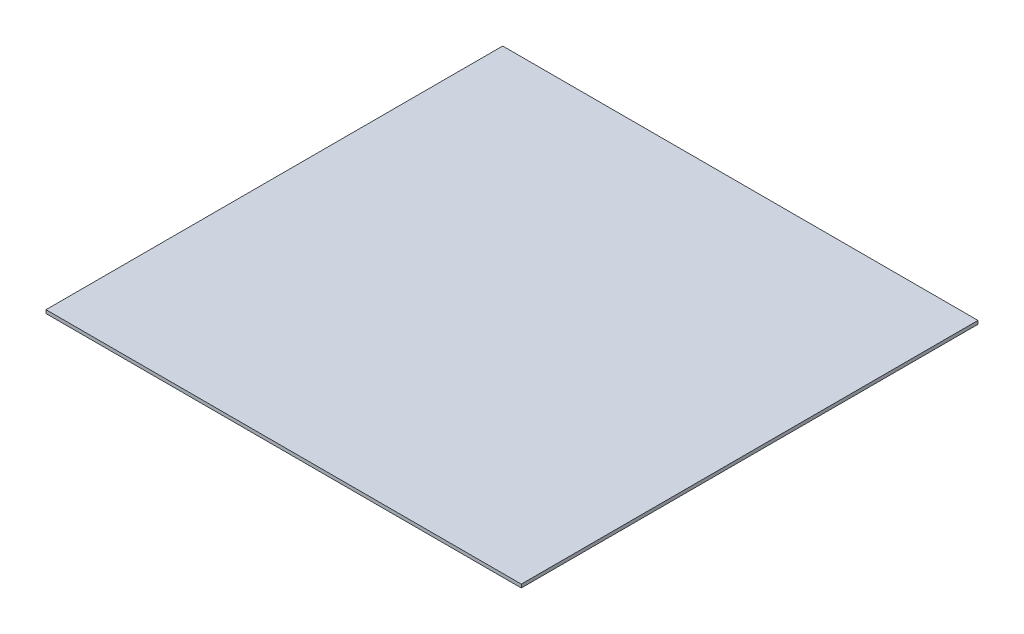
SolidWorks part; units mm, degrees
ref_plane "Front Plane" through (0, 0, 0) normal (0, 0, 1) x (1, 0, 0)
ref_plane "Top Plane" through (0, 0, 0) normal (0, 1, 0) x (1, 0, 0)
ref_plane "Right Plane" through (0, 0, 0) normal (1, 0, 0) x (0, 0, -1)
sketch "Sketch1" plane through (0, 0, 0) normal (0, 1, 0) x (1, 0, 0)
  line L1 (-281, 270) -> (281, 270)
  line L2 (-281, 270) -> (-281, -270)
  line L3 (-281, -270) -> (281, -270)
  line L4 (281, 270) -> (281, -270)
  line L5 (-281, 270) -> (281, -270) construction
  line L6 (-281, -270) -> (281, 270) construction
  point P0 (0, 0)
  dimension "D1" = 562
  dimension "D2" = 540
extrude "Boss-Extrude1" add sketch "Sketch1" along normal blind 4
